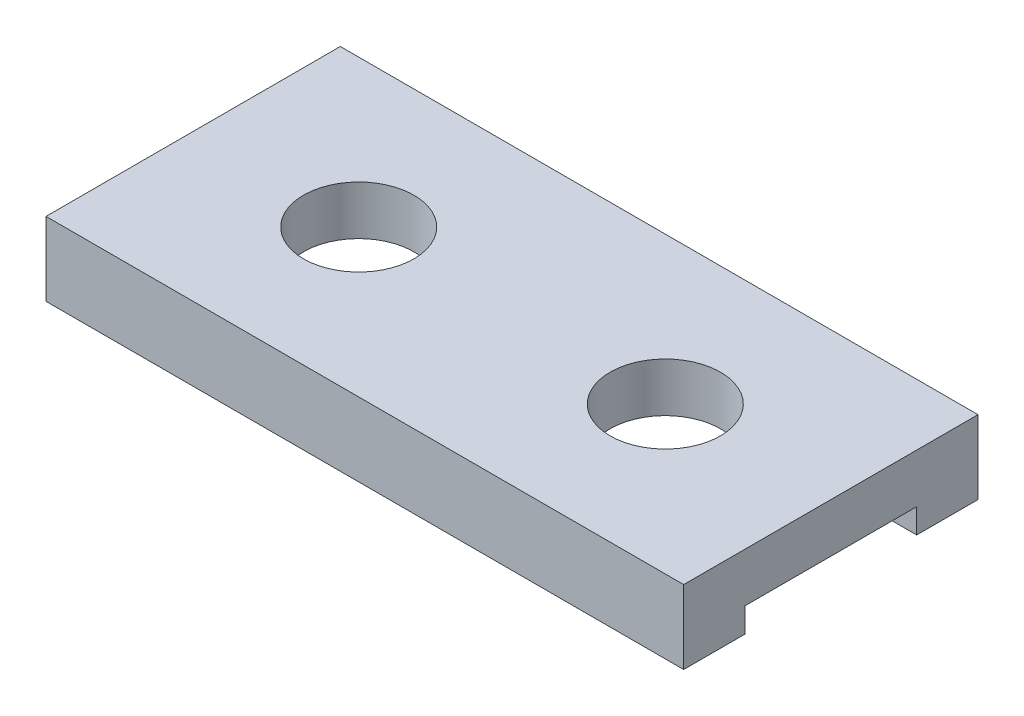
SolidWorks part; units mm, degrees
material "6061-T6 (SS)"
ref_plane "Front" through (0, 0, 0) normal (0, 0, 1) x (1, 0, 0)
ref_plane "Top" through (0, 0, 0) normal (0, 1, 0) x (1, 0, 0)
ref_plane "Right" through (0, 0, 0) normal (1, 0, 0) x (0, 0, -1)
sketch "Sketch1" plane through (0, 0, 0) normal (0, 1, 0) x (1, 0, 0)
  line L1 (-13, 6) -> (13, 6)
  line L2 (-13, 6) -> (-13, -6)
  line L3 (-13, -6) -> (13, -6)
  line L4 (13, 6) -> (13, -6)
  dimension "D1" = 13
  dimension "D2" = 13
  dimension "D3" = 6
  dimension "D4" = 6
extrude "Extrude1" add sketch "Sketch1" against normal blind 3
sketch "Sketch2" plane through (0, 0, 0) normal (0, 1, 0) x (1, 0, 0)
  circle A0 centre (-6.25, 0) radius 2.25
  circle A1 centre (6.25, 0) radius 2.25
  dimension "D3" = 4.5
  dimension "D4" = 4.5
  dimension "D1" = 6.25
  dimension "D2" = 6.25
extrude "Extrude2" cut sketch "Sketch2" against normal through all
sketch "Sketch3" plane through (13, 0, 0) normal (1, 0, 0) x (0, 0, -1)
  line L0 (-6, -3) -> (6, -3) construction
  line L1 (-3.5, -3) -> (3.5, -3)
  line L2 (-3.5, -3) -> (-3.5, -2)
  line L3 (-3.5, -2) -> (3.5, -2)
  line L4 (3.5, -3) -> (3.5, -2)
  line L5 (-6, -3) -> (-6, 0) construction
  line L6 (6, -3) -> (6, 0) construction
  dimension "D1" = 2.5
  dimension "D2" = 2.5
  dimension "D3" = 1
extrude "Extrude3" cut sketch "Sketch3" against normal through all
